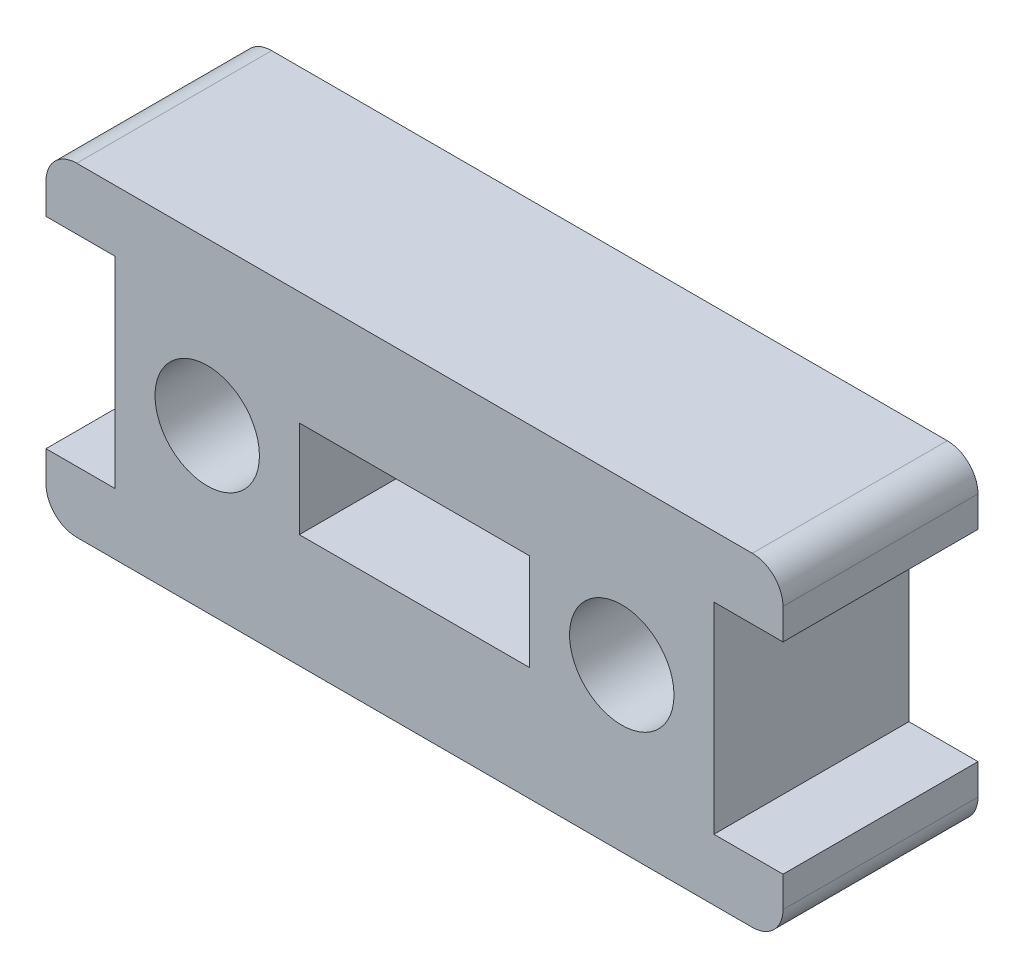
SolidWorks part; units mm, degrees
material "6061-T6 (SS)"
ref_plane "Front" through (0, 0, 0) normal (0, 0, 1) x (1, 0, 0)
ref_plane "Top" through (0, 0, 0) normal (0, 1, 0) x (1, 0, 0)
ref_plane "Right" through (0, 0, 0) normal (1, 0, 0) x (0, 0, -1)
sketch "Sketch1" plane through (0, 0, 0) normal (0, 0, 1) x (1, 0, 0)
  line L0 (0, 0) -> (-12.7, 0) construction
  line L1 (3.75, -1.575) -> (-3.75, -1.575) construction
  line L2 (3.75, -1.575) -> (3.75, 1.575) construction
  line L3 (3.75, 1.575) -> (-3.75, 1.575) construction
  line L4 (-3.75, -1.575) -> (-3.75, 1.575) construction
  line L5 (3.75, -1.575) -> (-3.75, 1.575) construction
  line L6 (3.75, 1.575) -> (-3.75, -1.575) construction
  line L7 (-12, 3.275) -> (-9.75, 3.275)
  line L8 (-12, -3.275) -> (-9.75, -3.275) construction
  line L9 (-12, -3.275) -> (-12, 3.275) construction
  line L10 (-12, 3.275) -> (-9.75, 3.275) construction
  line L11 (-9.75, -3.275) -> (-9.75, 3.275) construction
  line L12 (-12, -3.275) -> (-9.75, 3.275) construction
  line L13 (-12, 3.275) -> (-9.75, -3.275) construction
  line L14 (12.7, -5.275) -> (-12.7, -5.275) construction
  line L15 (12.7, -5.275) -> (12.7, 5.275) construction
  line L16 (12.7, 5.275) -> (-12.7, 5.275) construction
  line L17 (-12.7, -5.275) -> (-12.7, 5.275) construction
  line L18 (12.7, -5.275) -> (-12.7, 5.275) construction
  line L19 (12.7, 5.275) -> (-12.7, -5.275) construction
  line L20 (-9.75, 3.275) -> (-9.75, -3.275)
  line L21 (-9.75, -3.275) -> (-12, -3.275)
  line L22 (-12, -3.275) -> (-12, -5.275)
  line L23 (-12, -5.275) -> (12, -5.275)
  line L24 (0, -5.275) -> (0, 0) construction
  line L25 (-12, 3.275) -> (-12, 5.275)
  line L26 (-12, 5.275) -> (12, 5.275)
  line L27 (12, 3.275) -> (12, 5.275)
  line L28 (12, 3.275) -> (9.75, 3.275)
  line L29 (9.75, 3.275) -> (9.75, -3.275)
  line L30 (9.75, -3.275) -> (12, -3.275)
  line L31 (12, -3.275) -> (12, -5.275)
  line L33 (3.75, -1.575) -> (-3.75, -1.575)
  line L34 (3.75, -1.575) -> (3.75, 1.575)
  line L35 (3.75, 1.575) -> (-3.75, 1.575)
  line L36 (-3.75, -1.575) -> (-3.75, 1.575)
  line L37 (3.75, -1.575) -> (-3.75, 1.575) construction
  line L38 (3.75, 1.575) -> (-3.75, -1.575) construction
  circle A0 centre (-6.75, 0) radius 3 construction
  circle A1 centre (-6.75, 0) radius 1.6 construction
  circle A2 centre (6.75, 0) radius 1.6 construction
  point P0 (0, 0)
  point P11 (-10.875, 0)
  point P25 (0, 5.275)
  dimension "D3" = 6
  dimension "D4" = 3.2
  dimension "D1" = 7.5
  dimension "D2" = 3.15
  dimension "D5" = 6.55
  dimension "D6" = 2.25
  dimension "D7" = 2
  dimension "D8" = 25.4
  dimension "D9" = 19.5
  dimension "D10" = 24
  dimension "D11" = 10.55
extrude "Boss-Extrude1" add sketch "Sketch1" along normal blind 6.35
hole_wizard "M3 Clearance Hole1" positions "Sketch3" profile "Sketch2" hole size "M3" standard "ISO" end condition through all
sketch "Sketch3" plane through (0, 0, 6.35) normal (0, 0, 1) x (1, 0, 0)
  point P0 (-6.75, 0)
  point P3 (6.75, 0)
sketch "Sketch2" plane through (-6.75, 0, 6.35) normal (1, 0, 0) x (0, -1, 0)
  line L0 (0, 0) -> (0, 6.35)
  line L1 (0, 6.35) -> (1.7, 6.35)
  line L2 (1.7, 6.35) -> (1.7, 0)
  line L5 (1.7, 0) -> (0, 0)
  line L11 (0, -6.35) -> (0, 107.95) construction
  dimension "Thru Hole Dia." = 3.4
  dimension "Thru Hole Depth" = 6.35
fillet "Fillet1" radius 1 4 edges at (-12, -5.275, 3.175) (12, -5.275, 3.175) (12, 5.275, 3.175) (-12, 5.275, 3.175)
